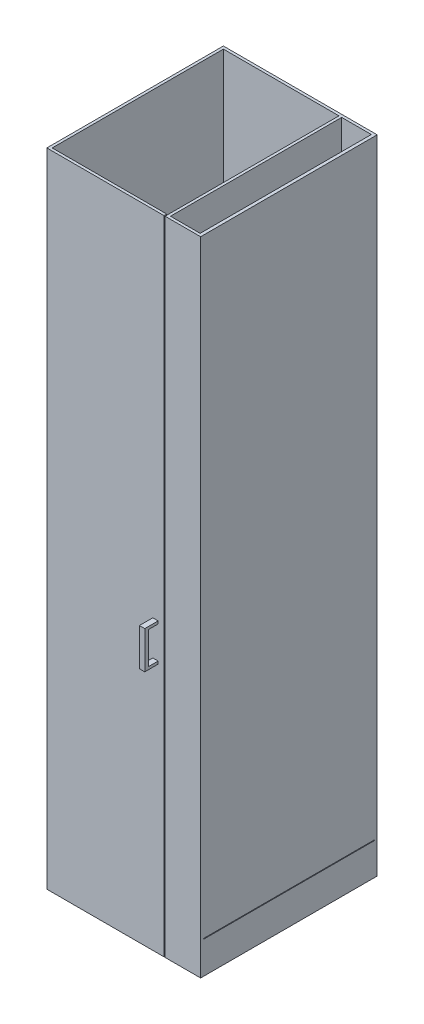
SolidWorks part; units mm, degrees
ref_plane "Front Plane" through (0, 0, 0) normal (0, 0, 1) x (1, 0, 0)
ref_plane "Top Plane" through (0, 0, 0) normal (0, 1, 0) x (1, 0, 0)
ref_plane "Right Plane" through (0, 0, 0) normal (1, 0, 0) x (0, 0, -1)
sketch "Sketch1" plane through (0, 0, 0) normal (0, 1, 0) x (1, 0, 0)
  line L0 (-138.29, -160) -> (-143.29, -160)
  line L1 (-138.29, 160) -> (138.29, 160)
  line L2 (-138.29, 160) -> (-138.29, -160)
  line L4 (138.29, 160) -> (138.29, -160)
  line L5 (-138.29, 160) -> (138.29, -160) construction
  line L6 (-138.29, -160) -> (138.29, 160) construction
  line L7 (-143.29, 165) -> (144.1741, 165)
  line L8 (-143.29, 165) -> (-143.29, -160)
  line L10 (144.1741, 165) -> (144.1741, -160)
  line L11 (-143.29, 165) -> (138.9479, -160) construction
  line L12 (-139.8052, -160) -> (144.1741, 165) construction
  line L13 (138.29, -160) -> (144.1741, -160)
  point P0 (0, 0)
  point P6 (0, 0)
  dimension "D1" = 320
  dimension "D2" = 276.58
  dimension "D3" = 5
  dimension "D4" = 5
  dimension "D5" = 325
extrude "Boss-Extrude1" add sketch "Sketch1" along normal blind 1200
sketch "Sketch3" plane through (0, 0, -160) normal (0, 0, 1) x (1, 0, 0)
  line L0 (-160.9848, 50) -> (150.3565, 50) construction
  line L1 (-138.29, 0) -> (138.29, 0) construction
  line L2 (138.29, 50) -> (-138.29, 178.9714)
  line L3 (138.29, 1200) -> (138.29, 0) construction
  line L4 (-138.29, 1200) -> (-138.29, 0) construction
  line L5 (-138.29, 178.9714) -> (-138.29, 188.9714)
  line L6 (-138.29, 1200) -> (-138.29, 0) construction
  line L7 (-138.29, 188.9714) -> (138.29, 60)
  line L8 (138.29, 60) -> (138.29, 50)
  dimension "D1" = 50
  dimension "D2" = 25
  dimension "D3" = 10
  dimension "D4" = 10
  dimension "D5" = 60
  dimension "D6" = 305.1723
extrude "Boss-Extrude2" add sketch "Sketch3" along normal up to surface (320 mm away) up to face at (141.232, 600, 160)
sketch "Sketch6" plane through (47.6808, 102.2518, 0) normal (0.4226, 0.9063, 0) x (0.9063, -0.4226, 0)
  line L1 (78.8683, 30) -> (-86.1317, 30)
  line L2 (78.8683, 30) -> (78.8683, -30)
  line L3 (78.8683, -30) -> (-86.1317, -30)
  line L4 (-86.1317, 30) -> (-86.1317, -30)
  dimension "D1" = 60
  dimension "D2" = 165
extrude "Cut-Extrude2" cut sketch "Sketch6" against normal blind 10 from offset 0.5
sketch "Sketch15" plane through (0, 0, -30) normal (0, 0, 1) x (1, 0, 0)
  line L0 (-30.9608, 128.9229) -> (-12.4111, 120.2731)
  line L1 (115.3295, 60.7066) -> (-34.2113, 130.4387) construction
  line L5 (-12.4111, 120.2731) -> (-12.4111, 105.2731)
  line L6 (-12.4111, 105.2731) -> (-30.9608, 113.9229)
  line L7 (-30.9608, 113.9229) -> (-30.9608, 128.9229)
  line L8 (138.29, 50) -> (-138.29, 178.9714) construction
  dimension "D1" = 15
extrude "Boss-Extrude14" add sketch "Sketch15" against normal blind 15
pattern_linear "LPattern1" count 2 spacing 136 along (0.9063, -0.4226, 0) of "Boss-Extrude14"
pattern_linear "LPattern2" count 2 spacing 75 along (0, 0, 1) of "LPattern1", "Boss-Extrude14"
sketch "Sketch14" plane through (0, 0, -30) normal (0, 0, 1) x (1, 0, 0)
  line L2 (-30.381, 138.6526) -> (119.1597, 68.9206) construction
  line L4 (-34.2113, 130.4387) -> (-30.381, 138.6526) construction
  line L6 (115.3295, 60.7066) -> (119.1597, 68.9206) construction
  circle A0 centre (-22.5223, 121.1958) radius 2.5
  circle A1 centre (100.7355, 63.7197) radius 2.5
  dimension "D1" = 5
  dimension "D3" = 5
  dimension "D2" = 12.5
  dimension "D4" = 12.5
  dimension "D5" = 14.5
  dimension "D6" = 14.5
extrude "Cut-Extrude5" cut sketch "Sketch14" against normal blind 80 from offset 70
sketch "Sketch19" plane through (0, 0, -160) normal (0, 0, 1) x (1, 0, 0)
  line L0 (139.3789, 431.0698) -> (82.7989, 431.0698) construction
  line L2 (82.7989, 85.8759) -> (82.7989, 1200)
  line L4 (-138.29, 1200) -> (138.29, 1200) construction
  line L5 (82.7989, 1200) -> (77.7989, 1200)
  line L6 (77.7989, 1200) -> (77.7989, 88.2075)
  line L7 (77.7989, 88.2075) -> (82.7989, 85.8759)
  line L9 (138.29, 60) -> (-138.29, 188.9714) construction
  dimension "D1" = 56.58
  dimension "D2" = 5
extrude "Boss-Extrude19" add sketch "Sketch19" along normal blind 320
sketch "Sketch27" plane through (0, 0, 160) normal (0, 0, 1) x (1, 0, 0)
  line L0 (77.7989, 97.5907) -> (82.7989, 95.2591)
  line L1 (77.7989, 1200) -> (77.7989, 88.2075) construction
  line L2 (82.7989, 85.8759) -> (82.7989, 1200) construction
  line L3 (82.7989, 95.2591) -> (82.7989, 85.8759)
  line L4 (82.7989, 85.8759) -> (77.7989, 88.7152)
  line L5 (77.7989, 1200) -> (77.7989, 88.2075) construction
  line L6 (77.7989, 88.7152) -> (77.7989, 97.5907)
  line L7 (82.7989, 85.8759) -> (138.29, 60) construction
extrude "Cut-Extrude10" cut sketch "Sketch27" against normal up to surface (320 mm away) up to face at (-30.2456, 669.2947, -160)
sketch "Sketch28" plane through (0, 0, 160) normal (0, 0, 1) x (1, 0, 0)
  line L0 (77.7989, 97.5907) -> (83.147, 87.4032)
  line L1 (83.147, 87.4032) -> (82.7989, 95.2591)
  line L2 (82.7989, 95.2591) -> (77.7989, 97.5907)
  line L3 (82.7989, 85.8759) -> (77.7989, 88.7152) construction
  dimension "D1" = 1.5
extrude "Boss-Extrude20" add sketch "Sketch28" against normal up to surface (320 mm away) up to face at (0, 57.2428, -160)
sketch "Sketch29" plane through (0, 0, 160) normal (0, 0, 1) x (1, 0, 0)
  line L0 (138.29, 60) -> (158.5697, 60) construction
  line L1 (138.29, 60) -> (138.29, 63)
  line L2 (138.29, 1200) -> (138.29, 60) construction
  line L3 (138.29, 63) -> (144.1741, 61.2)
  line L4 (144.1741, 1200) -> (144.1741, 0) construction
  line L5 (144.1741, 61.2) -> (144.1741, 60)
  line L6 (144.1741, 60) -> (138.29, 60)
  dimension "D1" = 1.2
  dimension "D2" = 3
extrude "Cut-Extrude11" cut sketch "Sketch29" against normal up to surface (320 mm away) up to face at (0, 57.2428, -160)
sketch "Sketch31" plane through (0, 0, 160) normal (0, 0, 1) x (1, 0, 0)
  line L0 (77.7989, 88.2075) -> (82.7989, 85.8759)
  line L1 (82.7989, 85.8759) -> (77.7989, 88.7152)
  line L2 (77.7989, 88.7152) -> (77.7989, 88.2075)
extrude "Cut-Extrude12" cut sketch "Sketch31" against normal up to surface (320 mm away) up to face at (0, 57.2428, -160)
sketch "Sketch32" plane through (0, 0, 160) normal (0, 0, 1) x (1, 0, 0)
  line L1 (77.7989, 1200) -> (144.1741, 1200)
  line L2 (77.7989, 1200) -> (77.7989, 0)
  line L3 (77.7989, 0) -> (144.1741, 0)
  line L4 (144.1741, 1200) -> (144.1741, 0)
extrude "Boss-Extrude21" add sketch "Sketch32" along normal blind 5
sketch "Sketch33" plane through (0, 0, 160) normal (0, 0, 1) x (1, 0, 0)
  line L5 (-138.29, 0) -> (138.29, 0) construction
  line L6 (-143.29, 1200) -> (75.7989, 1200)
  line L7 (-143.29, 1200) -> (-143.29, 0)
  line L8 (-143.29, 0) -> (75.7989, 0)
  line L9 (75.7989, 1200) -> (75.7989, 0)
  line L11 (77.7989, 1200) -> (77.7989, 97.5907) construction
  dimension "D1" = 2
extrude "Boss-Extrude23" add sketch "Sketch33" along normal blind 5
sketch "Sketch34" plane through (0, 0, 160) normal (0, 0, -1) x (-1, 0, 0)
  line L1 (-54.754, 538.3935) -> (-64.754, 538.3935)
  line L2 (-54.754, 538.3935) -> (-54.754, 468.3935)
  line L3 (-54.754, 468.3935) -> (-64.754, 468.3935)
  line L4 (-64.754, 538.3935) -> (-64.754, 468.3935)
  dimension "D1" = 70
  dimension "D2" = 10
extrude "Boss-Extrude24" add sketch "Sketch34" against normal blind 30
sketch "Sketch35" plane through (54.754, 0, 0) normal (-1, 0, 0) x (0, 0, 1)
  line L0 (165, 1200) -> (165, 0) construction
  line L1 (165, 533.3935) -> (183, 533.3935)
  line L2 (165, 533.3935) -> (165, 473.3935)
  line L3 (165, 473.3935) -> (183, 473.3935)
  line L4 (183, 533.3935) -> (183, 473.3935)
  line L5 (190, 538.3935) -> (165, 538.3935) construction
  line L6 (190, 468.3935) -> (190, 538.3935) construction
  line L7 (190, 468.3935) -> (165, 468.3935) construction
  dimension "D1" = 5
  dimension "D2" = 7
  dimension "D3" = 5
extrude "Cut-Extrude13" cut sketch "Sketch35" against normal up to next
